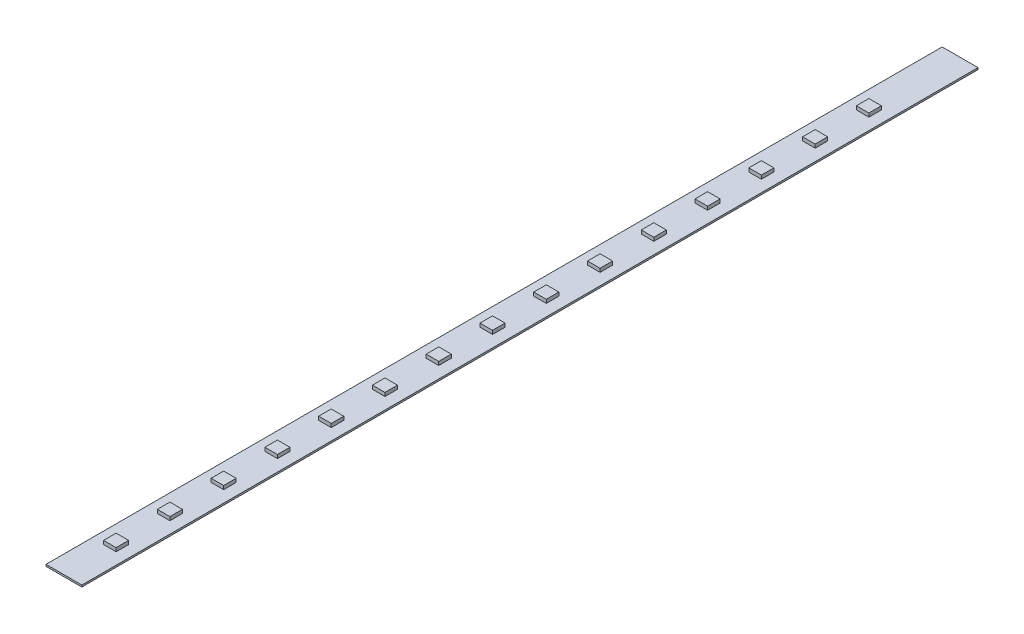
SolidWorks part; units mm, degrees
ref_plane "Plan de face" through (0, 0, 0) normal (0, 0, 1) x (1, 0, 0)
ref_plane "Plan de dessus" through (0, 0, 0) normal (0, 1, 0) x (1, 0, 0)
ref_plane "Plan de droite" through (0, 0, 0) normal (1, 0, 0) x (0, 0, -1)
sketch "Esquisse1" plane through (0, 0, 0) normal (0, 1, 0) x (1, 0, 0)
  line L0 (-10, 0) -> (10, 0) construction
  line L1 (-10, -250) -> (10, -250)
  line L2 (-10, -250) -> (-10, 250)
  line L3 (-10, 250) -> (10, 250)
  line L4 (10, -250) -> (10, 250)
  point P6 (0, 0)
  dimension "D1" = 20
  dimension "D2" = 500
extrude "Boss.-Extru.1" add sketch "Esquisse1" along normal blind 1
fillet "Congé1" [suppressed] radius 5
sketch "Esquisse2" plane through (0, 1, 0) normal (0, 1, 0) x (1, 0, 0)
  line L0 (0, -250) -> (0, 19.128) construction
  line L1 (3.5, 15.628) -> (-3.5, 15.628)
  line L2 (3.5, 15.628) -> (3.5, 22.628)
  line L3 (3.5, 22.628) -> (-3.5, 22.628)
  line L4 (-3.5, 15.628) -> (-3.5, 22.628)
  line L5 (3.5, 15.628) -> (-3.5, 22.628) construction
  line L6 (3.5, 22.628) -> (-3.5, 15.628) construction
  line L7 (-10, -250) -> (10, -250) construction
  point P0 (0, 19.128)
  dimension "D1" = 7
extrude "Boss.-Extru.2" add sketch "Esquisse2" along normal blind 2
pattern_linear "Répétition linéaire1" count 7 spacing 30 along (0, 0, -1) count 9 spacing 30 along (0, 0, 1) of "Boss.-Extru.2"
